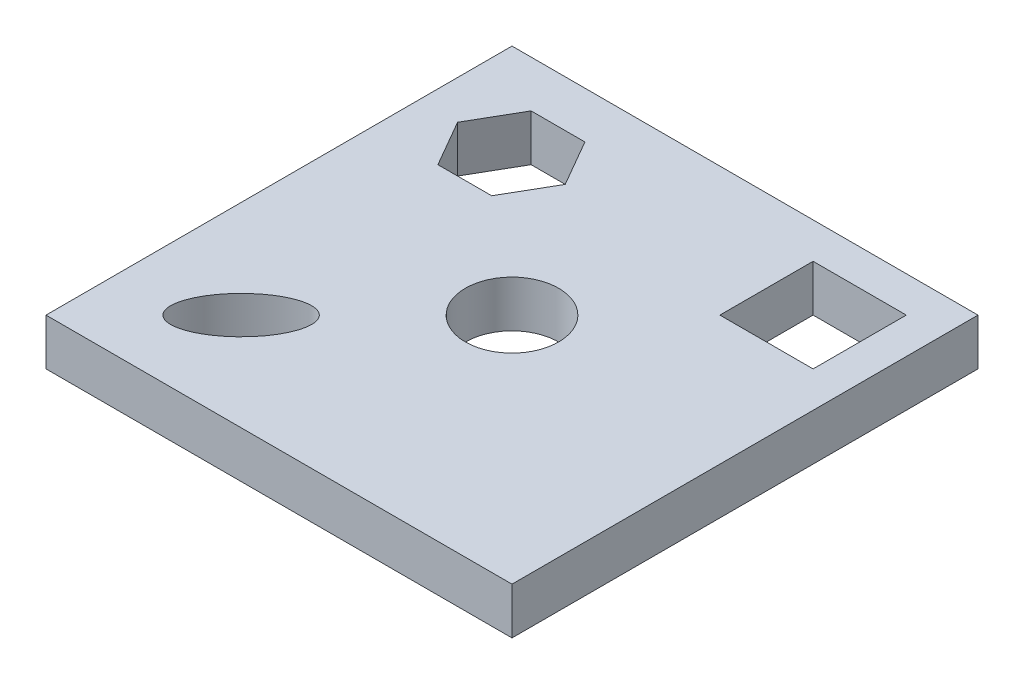
SolidWorks part; units mm, degrees
ref_plane "Front Plane" through (0, 0, 0) normal (0, 0, 1) x (1, 0, 0)
ref_plane "Top Plane" through (0, 0, 0) normal (0, 1, 0) x (1, 0, 0)
ref_plane "Right Plane" through (0, 0, 0) normal (1, 0, 0) x (0, 0, -1)
sketch "Sketch1" plane through (0, 0, 0) normal (0, 1, 0) x (1, 0, 0)
  line L2 (-50, -50) -> (50, -50)
  line L3 (-50, -50) -> (-50, 50)
  line L4 (-50, 50) -> (50, 50)
  line L5 (50, -50) -> (50, 50)
  line L6 (-50, -50) -> (50, 50) construction
  line L7 (-50, 50) -> (50, -50) construction
  line L8 (-18.5816, 30) -> (-24.3551, 40)
  line L9 (-24.3551, 40) -> (-35.9021, 40)
  line L10 (-35.9021, 40) -> (-41.6756, 30)
  line L11 (-41.6756, 30) -> (-35.9021, 20)
  line L12 (-35.9021, 20) -> (-24.3551, 20)
  line L13 (-24.3551, 20) -> (-18.5816, 30)
  line L14 (22.3058, 22.3058) -> (42.3058, 22.3058)
  line L15 (22.3058, 22.3058) -> (22.3058, 42.3058)
  line L16 (22.3058, 42.3058) -> (42.3058, 42.3058)
  line L17 (42.3058, 22.3058) -> (42.3058, 42.3058)
  line L18 (22.3058, 22.3058) -> (42.3058, 42.3058) construction
  line L19 (22.3058, 42.3058) -> (42.3058, 22.3058) construction
  circle A0 centre (0, 0) radius 10
  circle A1 centre (-30.1286, 30) radius 10 construction
  ellipse E0 centre (-29.0651, -29.0651) end of major axis (-20.6738, -20.6738) minor radius 5.7172
  point P0 (0, 0)
  point P9 (32.3058, 32.3058)
  point P22 (0, 0)
  point P28 (0, 0)
  point P29 (42.3058, 32.3058)
  dimension "D3" = 20
  dimension "D4" = 20
  dimension "D1" = 100
  dimension "D2" = 100
  dimension "D5" = 30
  dimension "D6" = 19.8714
  dimension "D7" = 20
  dimension "D8" = 7.6942
  dimension "D9" = 16.7826
  dimension "D10" = 11.4343
  dimension "D11" = 20.9349
extrude "Boss-Extrude1" add sketch "Sketch1" along normal blind 10
